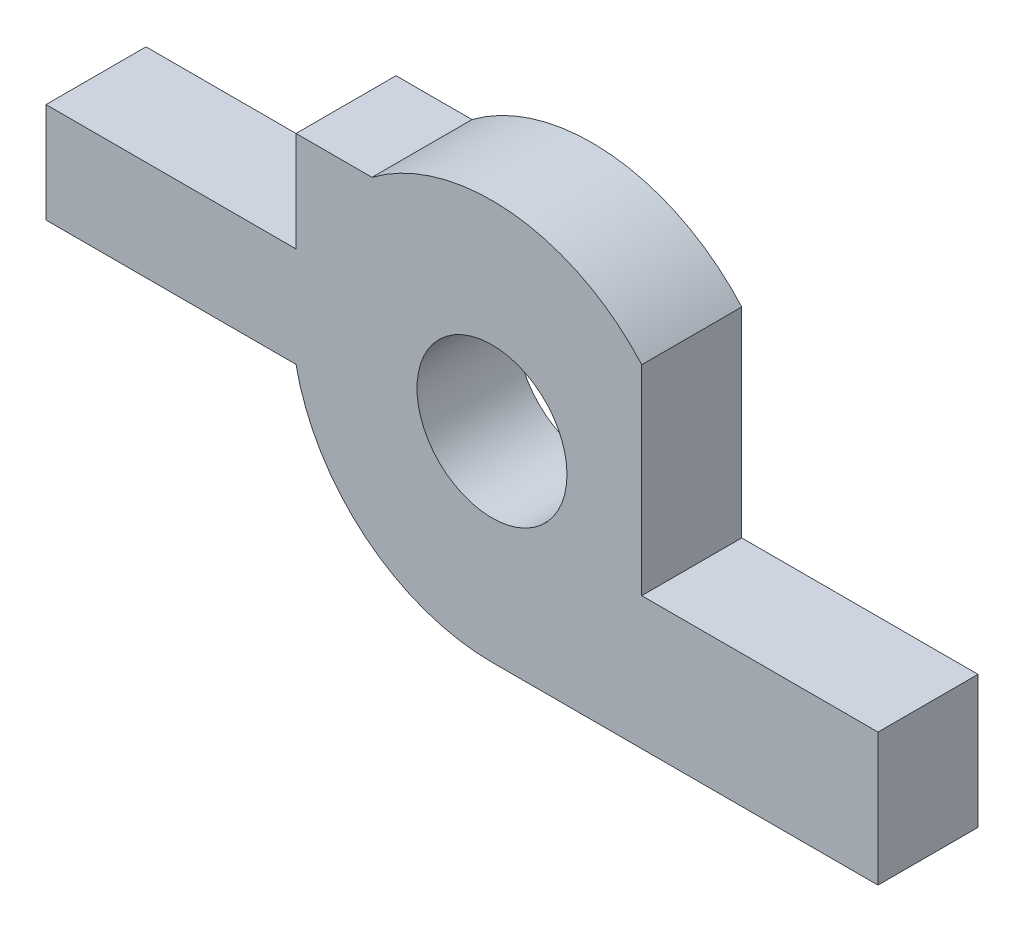
SolidWorks part; units mm, degrees
ref_plane "Front Plane" through (0, 0, 0) normal (0, 0, 1) x (1, 0, 0)
ref_plane "Top Plane" through (0, 0, 0) normal (0, 1, 0) x (1, 0, 0)
ref_plane "Right Plane" through (0, 0, 0) normal (1, 0, 0) x (0, 0, -1)
sketch "Sketch1" plane through (0, 0, 0) normal (0, 0, 1) x (1, 0, 0)
  line L0 (7.72, -4) -> (0, -4)
  line L1 (-3.9192, 1.2) -> (-3.9192, 3.2)
  line L2 (7.72, -1.3485) -> (7.72, -4)
  line L3 (-3.9192, -0.8) -> (-8.9192, -0.8)
  line L4 (2.9949, 2.6515) -> (2.9949, -1.3485)
  line L5 (-8.9192, 1.2) -> (-8.9192, -0.8)
  line L6 (2.9949, -1.3485) -> (7.72, -1.3485)
  line L7 (-3.9192, 1.2) -> (-8.9192, 1.2)
  line L11 (-3.9192, 3.2) -> (-2.4, 3.2)
  circle A0 centre (0, 0) radius 1.5
  arc A1 (2.9949, 2.6515) -> (-2.4, 3.2) centre (0, 0) ccw
  arc A3 (-3.9192, -0.8) -> (0, -4) centre (0, 0) ccw
  dimension "D1" = 3
  dimension "D2" = 4
  dimension "D4" = 7.72
  dimension "D3" = 2.9949
  dimension "D5" = 2.4
  dimension "D6" = 3.9192
  dimension "D7" = 8.9192
  dimension "D8" = 1.3485
extrude "Boss-Extrude1" add sketch "Sketch1" along normal blind 2
